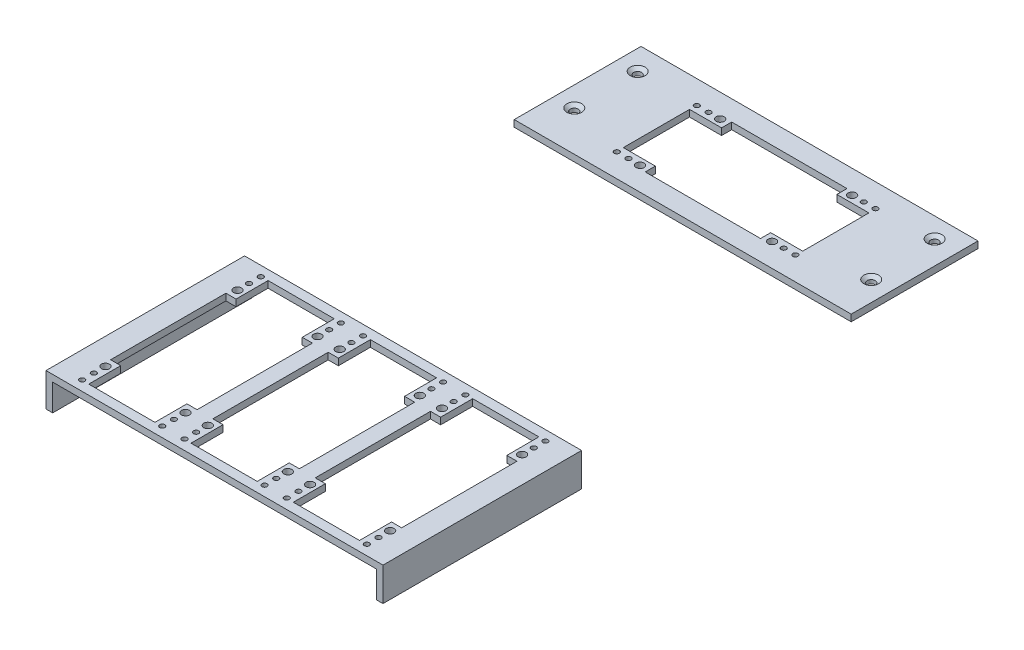
SolidWorks part; units mm, degrees
ref_plane "Front Plane" through (0, 0, 0) normal (0, 0, 1) x (1, 0, 0)
ref_plane "Top Plane" through (0, 0, 0) normal (0, 1, 0) x (1, 0, 0)
ref_plane "Right Plane" through (0, 0, 0) normal (1, 0, 0) x (0, 0, -1)
sketch "Sketch1" plane through (0, 0, 0) normal (0, 1, 0) x (1, 0, 0)
  line L0 (37.4967, 30.1625) -> (0, 30.1625) construction
  line L1 (0, 0) -> (160.3375, 0)
  line L2 (0, 0) -> (0, 60.325)
  line L3 (0, 60.325) -> (160.3375, 60.325)
  line L4 (160.3375, 0) -> (160.3375, 60.325)
  line L5 (122.8408, 30.1625) -> (160.3375, 30.1625) construction
  line L6 (80.1687, 50.7365) -> (80.1687, 60.325) construction
  line L7 (80.1687, 9.5885) -> (80.1687, 0) construction
  line L8 (29.5195, -167.5613) -> (-7.9773, -167.5613) construction
  line L9 (-7.9773, -214.8053) -> (152.3602, -214.8053)
  line L10 (-7.9773, -214.8053) -> (-7.9773, -120.3173)
  line L11 (-7.9773, -120.3173) -> (152.3602, -120.3173)
  line L12 (152.3602, -214.8053) -> (152.3602, -120.3173)
  line L13 (114.8635, -167.5613) -> (152.3602, -167.5613) construction
  line L14 (72.1915, -129.9058) -> (72.1915, -120.3173) construction
  line L15 (72.1915, -205.2168) -> (72.1915, -214.8053) construction
  circle A0 centre (9.525, 49.2125) radius 0.254
  circle A1 centre (9.525, 19.05) radius 0.254
  circle A2 centre (149.225, 50.8) radius 0.254
  circle A3 centre (150.8125, 19.05) radius 0.254
  point P13 (9.525, 49.2125)
  point P14 (9.525, 19.05)
  point P15 (150.8125, 19.05)
  point P16 (149.225, 50.8)
  dimension "D11" = 160.3375
  dimension "D1" = 160.3375
  dimension "D2" = 60.325
  dimension "D3" = 11.1125
  dimension "D4" = 9.525
  dimension "D5" = 9.525
  dimension "D6" = 19.05
  dimension "D7" = 9.525
  dimension "D8" = 11.1125
  dimension "D9" = 9.525
  dimension "D10" = 19.05
  dimension "D12" = 94.488
extrude "Boss-Extrude1" add sketch "Sketch1" along normal blind 3.175
hole_wizard "CSK for #6 Flat Head Machine Screw (100)2" positions "Sketch11" profile "Sketch12" countersink size "#6" standard "ANSI Inch" end condition through all
sketch "Sketch11" plane through (0, 3.175, 0) normal (0, 1, 0) x (1, 0, 0)
  point P0 (9.525, 49.2125)
  point P3 (9.525, 19.05)
  point P6 (149.225, 50.8)
  point P9 (150.8125, 19.05)
sketch "Sketch12" plane through (9.525, 3.175, -49.2125) normal (1, 0, 0) x (0, 0, 1)
  line L0 (0, 0) -> (0, 3.175)
  line L1 (0, 3.175) -> (1.8986, 3.175)
  line L2 (1.8986, 3.175) -> (1.8986, 1.38)
  line L3 (1.8986, 1.38) -> (3.5433, 0)
  line L5 (3.5433, 0) -> (0, 0)
  line L6 (-1.8986, 1.38) -> (-3.5433, 0) construction
  line L11 (0, -6.35) -> (0, 107.95) construction
  dimension "Thru Hole Dia." = 3.7973
  dimension "Thru Hole Depth" = 3.175
  dimension "Near C'Sink Dia." = 7.0866
  dimension "Near C'Sink Angle" = 100
sketch "Sketch14" plane through (0, 3.175, 0) normal (0, 1, 0) x (1, 0, 0)
  line L0 (37.4968, 30.1625) -> (0, 30.1625) construction
  line L1 (152.3602, -120.3173) -> (-7.9773, -120.3173) construction
  line L2 (0, 60.325) -> (0, 0) construction
  line L4 (122.8407, 30.1625) -> (160.3375, 30.1625) construction
  line L6 (160.3375, 0) -> (160.3375, 60.325) construction
  line L8 (80.1688, 50.7365) -> (80.1688, 60.325) construction
  line L9 (160.3375, 60.325) -> (0, 60.325) construction
  line L10 (80.1688, 9.5885) -> (80.1688, 0) construction
  line L11 (0, 0) -> (160.3375, 0) construction
  line L12 (44.0928, -167.5613) -> (51.6175, -167.5613) construction
  line L13 (92.7655, -167.5613) -> (100.2901, -167.5613) construction
  line L14 (2.9448, -167.5613) -> (-7.9773, -167.5613) construction
  line L15 (-7.9773, -120.3173) -> (-7.9773, -214.8053) construction
  line L16 (141.4381, -167.5613) -> (152.3602, -167.5613) construction
  line L17 (152.3602, -214.8053) -> (152.3602, -120.3173) construction
  line L18 (72.1915, -124.8893) -> (72.1915, -120.3173)
  line L20 (72.1915, -210.2333) -> (72.1915, -214.8053)
  line L23 (-7.9773, -214.8053) -> (152.3602, -214.8053) construction
  point P30 (0, 0)
  line B0 (7.7708, -124.8893) -> (39.2668, -124.8893)
  line B1 (7.7708, -124.8893) -> (7.7708, -140.1293)
  line B2 (7.7708, -140.1293) -> (2.9448, -140.1293)
  line B3 (2.9448, -140.1293) -> (2.9448, -194.9933)
  line B4 (2.9448, -194.9933) -> (7.7708, -194.9933)
  line B5 (7.7708, -194.9933) -> (7.7708, -210.2333)
  line B6 (7.7708, -210.2333) -> (39.2668, -210.2333)
  line B7 (39.2668, -210.2333) -> (39.2668, -194.9933)
  line B8 (39.2668, -194.9933) -> (44.0928, -194.9933)
  line B9 (44.0928, -194.9933) -> (44.0928, -140.1293)
  line B10 (44.0928, -140.1293) -> (39.2668, -140.1293)
  line B11 (39.2668, -140.1293) -> (39.2668, -124.8893)
  line B12 (42.5688, -138.0719) -> (42.5688, -140.1293) construction
  line B13 (4.4688, -136.8785) -> (4.4688, -138.9359) construction
  circle B14 centre (4.4688, -198.9557) radius 1.905
  circle B15 centre (42.5688, -136.1669) radius 1.905
  circle B16 centre (4.4688, -136.1669) radius 1.905
  circle B17 centre (4.4688, -204.4929) radius 1.2192
  circle B18 centre (4.4688, -210.0555) radius 1.2192
  circle B19 centre (42.5688, -198.9557) radius 1.905
  circle B20 centre (42.5688, -204.4929) radius 1.2192
  circle B21 centre (42.5688, -210.0555) radius 1.2192
  circle B22 centre (42.5688, -130.6297) radius 1.2192
  circle B23 centre (42.5688, -125.0671) radius 1.2192
  circle B24 centre (4.4688, -130.6297) radius 1.2192
  circle B25 centre (4.4688, -125.0671) radius 1.2192
  line B26 (122.8408, 45.9105) -> (122.8408, 14.4145)
  line B27 (122.8408, 45.9105) -> (107.6007, 45.9105)
  line B28 (107.6007, 45.9105) -> (107.6007, 50.7365)
  line B29 (107.6007, 50.7365) -> (52.7368, 50.7365)
  line B30 (52.7368, 50.7365) -> (52.7368, 45.9105)
  line B31 (52.7368, 45.9105) -> (37.4967, 45.9105)
  line B32 (37.4967, 45.9105) -> (37.4968, 14.4145)
  line B33 (37.4968, 14.4145) -> (52.7368, 14.4145)
  line B34 (52.7368, 14.4145) -> (52.7368, 9.5885)
  line B35 (52.7368, 9.5885) -> (107.6008, 9.5885)
  line B36 (107.6008, 9.5885) -> (107.6008, 14.4145)
  line B37 (107.6008, 14.4145) -> (122.8408, 14.4145)
  line B38 (109.6582, 11.1125) -> (107.6008, 11.1125) construction
  line B39 (110.8515, 49.2125) -> (108.7941, 49.2125) construction
  circle B40 centre (48.7744, 49.2125) radius 1.905
  circle B41 centre (111.5632, 11.1125) radius 1.905
  circle B42 centre (111.5631, 49.2125) radius 1.905
  circle B43 centre (43.2372, 49.2125) radius 1.2192
  circle B44 centre (37.6746, 49.2125) radius 1.2192
  circle B45 centre (48.7744, 11.1125) radius 1.905
  circle B46 centre (43.2372, 11.1125) radius 1.2192
  circle B47 centre (37.6746, 11.1125) radius 1.2192
  circle B48 centre (117.1004, 11.1125) radius 1.2192
  circle B49 centre (122.663, 11.1125) radius 1.2192
  circle B50 centre (117.1003, 49.2125) radius 1.2192
  circle B51 centre (122.6629, 49.2125) radius 1.2192
  line B52 (56.4435, -124.8893) -> (87.9395, -124.8893)
  line B53 (56.4435, -124.8893) -> (56.4435, -140.1293)
  line B54 (56.4435, -140.1293) -> (51.6175, -140.1293)
  line B55 (51.6175, -140.1293) -> (51.6175, -194.9933)
  line B56 (51.6175, -194.9933) -> (56.4435, -194.9933)
  line B57 (56.4435, -194.9933) -> (56.4435, -210.2333)
  line B58 (56.4435, -210.2333) -> (87.9395, -210.2333)
  line B59 (87.9395, -210.2333) -> (87.9395, -194.9933)
  line B60 (87.9395, -194.9933) -> (92.7655, -194.9933)
  line B61 (92.7655, -194.9933) -> (92.7655, -140.1293)
  line B62 (92.7655, -140.1293) -> (87.9395, -140.1293)
  line B63 (87.9395, -140.1293) -> (87.9395, -124.8893)
  line B64 (91.2415, -138.0719) -> (91.2415, -140.1293) construction
  line B65 (53.1415, -136.8785) -> (53.1415, -138.9359) construction
  circle B66 centre (53.1415, -198.9557) radius 1.905
  circle B67 centre (91.2415, -136.1669) radius 1.905
  circle B68 centre (53.1415, -136.1669) radius 1.905
  circle B69 centre (53.1415, -204.4929) radius 1.2192
  circle B70 centre (53.1415, -210.0555) radius 1.2192
  circle B71 centre (91.2415, -198.9557) radius 1.905
  circle B72 centre (91.2415, -204.4929) radius 1.2192
  circle B73 centre (91.2415, -210.0555) radius 1.2192
  circle B74 centre (91.2415, -130.6297) radius 1.2192
  circle B75 centre (91.2415, -125.0671) radius 1.2192
  circle B76 centre (53.1415, -130.6297) radius 1.2192
  circle B77 centre (53.1415, -125.0671) radius 1.2192
  line B78 (105.1161, -124.8893) -> (136.6121, -124.8893)
  line B79 (105.1161, -124.8893) -> (105.1161, -140.1293)
  line B80 (105.1161, -140.1293) -> (100.2901, -140.1293)
  line B81 (100.2901, -140.1293) -> (100.2901, -194.9933)
  line B82 (100.2901, -194.9933) -> (105.1161, -194.9933)
  line B83 (105.1161, -194.9933) -> (105.1161, -210.2333)
  line B84 (105.1161, -210.2333) -> (136.6121, -210.2333)
  line B85 (136.6121, -210.2333) -> (136.6121, -194.9933)
  line B86 (136.6121, -194.9933) -> (141.4381, -194.9933)
  line B87 (141.4381, -194.9933) -> (141.4381, -140.1293)
  line B88 (141.4381, -140.1293) -> (136.6121, -140.1293)
  line B89 (136.6121, -140.1293) -> (136.6121, -124.8893)
  line B90 (139.9141, -138.0719) -> (139.9141, -140.1293) construction
  line B91 (101.8141, -136.8785) -> (101.8141, -138.9359) construction
  circle B92 centre (101.8141, -198.9557) radius 1.905
  circle B93 centre (139.9141, -136.1669) radius 1.905
  circle B94 centre (101.8141, -136.1669) radius 1.905
  circle B95 centre (101.8141, -204.4929) radius 1.2192
  circle B96 centre (101.8141, -210.0555) radius 1.2192
  circle B97 centre (139.9141, -198.9557) radius 1.905
  circle B98 centre (139.9141, -204.4929) radius 1.2192
  circle B99 centre (139.9141, -210.0555) radius 1.2192
  circle B100 centre (139.9141, -130.6297) radius 1.2192
  circle B101 centre (139.9141, -125.0671) radius 1.2192
  circle B102 centre (101.8141, -130.6297) radius 1.2192
  circle B103 centre (101.8141, -125.0671) radius 1.2192
sketch_block_instance "Block3-1"
sketch_block "Block3" parameters "D7"=2.4384, "D14"=3.81, "D1"=85.344, "D2"=31.496, "D3"=38.1, "D4"=62.7888, "D5"=5.5372, "D6"=5.5626, "D8"=5.5372, "D9"=5.5626, "D10"=5.5372, "D11"=5.5372, "D12"=4.826, "D13"=3.302, "D15"=5.5626
sketch_block_instance "Block3-2"
sketch_block_instance "Block3-4"
sketch_block_instance "Block3-5"
sketch "Sketch15" plane through (0, 0, 0) normal (0, -1, 0) x (-1, 0, 0)
  line L0 (7.9773, -214.8053) -> (-152.3602, -214.8053) construction
  line L1 (-152.3602, -120.3173) -> (-149.1852, -120.3173)
  line L2 (-152.3602, -120.3173) -> (-152.3602, -214.8053)
  line L3 (-152.3602, -214.8053) -> (-149.1852, -214.8053)
  line L4 (-149.1852, -120.3173) -> (-149.1852, -214.8053)
  line L6 (7.9773, -120.3173) -> (4.8023, -120.3173)
  line L7 (7.9773, -120.3173) -> (7.9773, -214.8053)
  line L8 (7.9773, -214.8053) -> (4.8023, -214.8053)
  line L9 (4.8023, -120.3173) -> (4.8023, -214.8053)
  dimension "D1" = 3.175
extrude "Boss-Extrude2" add sketch "Sketch15" along normal blind 12.7
sketch "Sketch19" plane through (0, 3.175, 0) normal (0, 1, 0) x (1, 0, 0)
  line L0 (7.7708, -124.8893) -> (39.2668, -124.8893) construction
  line L1 (7.7708, -210.2333) -> (39.2668, -210.2333) construction
  line L2 (7.7708, -194.9933) -> (7.7708, -210.2333) construction
  line L3 (2.9448, -194.9933) -> (7.7708, -194.9933) construction
  line L4 (39.2668, -210.2333) -> (39.2668, -194.9933) construction
  line L5 (39.2668, -194.9933) -> (44.0928, -194.9933) construction
  line L6 (44.0928, -194.9933) -> (44.0928, -140.1293) construction
  line L7 (44.0928, -140.1293) -> (39.2668, -140.1293) construction
  line L8 (39.2668, -140.1293) -> (39.2668, -124.8893) construction
  line L9 (7.7708, -124.8893) -> (7.7708, -140.1293) construction
  line L10 (7.7708, -140.1293) -> (2.9448, -140.1293) construction
  line L11 (2.9448, -140.1293) -> (2.9448, -194.9933) construction
  line L12 (7.7708, -124.8893) -> (39.2668, -124.8893)
  line L13 (7.7708, -210.2333) -> (39.2668, -210.2333)
  line L14 (7.7708, -194.9933) -> (7.7708, -210.2333)
  line L15 (2.9448, -194.9933) -> (7.7708, -194.9933)
  line L16 (39.2668, -210.2333) -> (39.2668, -194.9933)
  line L17 (39.2668, -194.9933) -> (44.0928, -194.9933)
  line L18 (44.0928, -194.9933) -> (44.0928, -140.1293)
  line L19 (44.0928, -140.1293) -> (39.2668, -140.1293)
  line L20 (39.2668, -140.1293) -> (39.2668, -124.8893)
  line L21 (7.7708, -124.8893) -> (7.7708, -140.1293)
  line L22 (7.7708, -140.1293) -> (2.9448, -140.1293)
  line L23 (2.9448, -140.1293) -> (2.9448, -194.9933)
  line L24 (141.4381, -140.1293) -> (136.6121, -140.1293) construction
  line L25 (136.6121, -140.1293) -> (136.6121, -124.8893) construction
  line L26 (105.1161, -124.8893) -> (136.6121, -124.8893) construction
  line L27 (105.1161, -124.8893) -> (105.1161, -140.1293) construction
  line L28 (105.1161, -140.1293) -> (100.2901, -140.1293) construction
  line L29 (136.6121, -194.9933) -> (141.4381, -194.9933) construction
  line L30 (141.4381, -194.9933) -> (141.4381, -140.1293) construction
  line L31 (136.6121, -210.2333) -> (136.6121, -194.9933) construction
  line L32 (100.2901, -140.1293) -> (100.2901, -194.9933) construction
  line L33 (100.2901, -194.9933) -> (105.1161, -194.9933) construction
  line L34 (105.1161, -194.9933) -> (105.1161, -210.2333) construction
  line L35 (105.1161, -210.2333) -> (136.6121, -210.2333) construction
  line L36 (56.4435, -210.2333) -> (87.9395, -210.2333) construction
  line L37 (87.9395, -210.2333) -> (87.9395, -194.9933) construction
  line L38 (56.4435, -194.9933) -> (56.4435, -210.2333) construction
  line L39 (51.6175, -194.9933) -> (56.4435, -194.9933) construction
  line L40 (87.9395, -194.9933) -> (92.7655, -194.9933) construction
  line L41 (51.6175, -140.1293) -> (51.6175, -194.9933) construction
  line L42 (92.7655, -194.9933) -> (92.7655, -140.1293) construction
  line L43 (92.7655, -140.1293) -> (87.9395, -140.1293) construction
  line L44 (87.9395, -140.1293) -> (87.9395, -124.8893) construction
  line L45 (56.4435, -124.8893) -> (56.4435, -140.1293) construction
  line L46 (56.4435, -140.1293) -> (51.6175, -140.1293) construction
  line L47 (56.4435, -124.8893) -> (87.9395, -124.8893) construction
  line L48 (141.4381, -140.1293) -> (136.6121, -140.1293)
  line L49 (136.6121, -140.1293) -> (136.6121, -124.8893)
  line L50 (105.1161, -124.8893) -> (136.6121, -124.8893)
  line L51 (105.1161, -124.8893) -> (105.1161, -140.1293)
  line L52 (105.1161, -140.1293) -> (100.2901, -140.1293)
  line L53 (136.6121, -194.9933) -> (141.4381, -194.9933)
  line L54 (141.4381, -194.9933) -> (141.4381, -140.1293)
  line L55 (136.6121, -210.2333) -> (136.6121, -194.9933)
  line L56 (100.2901, -140.1293) -> (100.2901, -194.9933)
  line L57 (100.2901, -194.9933) -> (105.1161, -194.9933)
  line L58 (105.1161, -194.9933) -> (105.1161, -210.2333)
  line L59 (105.1161, -210.2333) -> (136.6121, -210.2333)
  line L60 (56.4435, -210.2333) -> (87.9395, -210.2333)
  line L61 (87.9395, -210.2333) -> (87.9395, -194.9933)
  line L62 (56.4435, -194.9933) -> (56.4435, -210.2333)
  line L63 (51.6175, -194.9933) -> (56.4435, -194.9933)
  line L64 (87.9395, -194.9933) -> (92.7655, -194.9933)
  line L65 (51.6175, -140.1293) -> (51.6175, -194.9933)
  line L66 (92.7655, -194.9933) -> (92.7655, -140.1293)
  line L67 (92.7655, -140.1293) -> (87.9395, -140.1293)
  line L68 (87.9395, -140.1293) -> (87.9395, -124.8893)
  line L69 (56.4435, -124.8893) -> (56.4435, -140.1293)
  line L70 (56.4435, -140.1293) -> (51.6175, -140.1293)
  line L71 (56.4435, -124.8893) -> (87.9395, -124.8893)
  line L72 (122.8408, 45.9105) -> (107.6007, 45.9105) construction
  line L73 (122.8408, 45.9105) -> (122.8408, 14.4145) construction
  line L74 (107.6008, 14.4145) -> (122.8408, 14.4145) construction
  line L75 (107.6008, 9.5885) -> (107.6008, 14.4145) construction
  line L76 (52.7368, 9.5885) -> (107.6008, 9.5885) construction
  line L77 (52.7368, 14.4145) -> (52.7368, 9.5885) construction
  line L78 (37.4968, 14.4145) -> (52.7368, 14.4145) construction
  line L79 (37.4967, 45.9105) -> (37.4968, 14.4145) construction
  line L80 (52.7368, 45.9105) -> (37.4967, 45.9105) construction
  line L81 (52.7368, 50.7365) -> (52.7368, 45.9105) construction
  line L82 (107.6007, 50.7365) -> (52.7368, 50.7365) construction
  line L83 (122.8408, 45.9105) -> (107.6007, 45.9105)
  line L84 (122.8408, 45.9105) -> (122.8408, 14.4145)
  line L85 (107.6008, 14.4145) -> (122.8408, 14.4145)
  line L86 (107.6008, 9.5885) -> (107.6008, 14.4145)
  line L87 (52.7368, 9.5885) -> (107.6008, 9.5885)
  line L88 (52.7368, 14.4145) -> (52.7368, 9.5885)
  line L89 (37.4968, 14.4145) -> (52.7368, 14.4145)
  line L90 (37.4967, 45.9105) -> (37.4968, 14.4145)
  line L91 (52.7368, 45.9105) -> (37.4967, 45.9105)
  line L92 (52.7368, 50.7365) -> (52.7368, 45.9105)
  line L93 (107.6007, 50.7365) -> (52.7368, 50.7365)
  line L94 (107.6007, 45.9105) -> (107.6007, 50.7365) construction
  line L95 (107.6007, 45.9105) -> (107.6007, 50.7365)
  circle A0 centre (42.5688, -136.1669) radius 1.905 construction
  circle A1 centre (42.5688, -130.6297) radius 1.2192 construction
  circle A2 centre (42.5688, -125.0671) radius 1.2192 construction
  circle A3 centre (4.4688, -136.1669) radius 1.905 construction
  circle A4 centre (4.4688, -130.6297) radius 1.2192 construction
  circle A5 centre (4.4688, -125.0671) radius 1.2192 construction
  circle A6 centre (42.5688, -210.0555) radius 1.2192 construction
  circle A7 centre (42.5688, -204.4929) radius 1.2192 construction
  circle A8 centre (42.5688, -198.9557) radius 1.905 construction
  circle A9 centre (4.4688, -210.0555) radius 1.2192 construction
  circle A10 centre (4.4688, -204.4929) radius 1.2192 construction
  circle A11 centre (4.4688, -198.9557) radius 1.905 construction
  circle A12 centre (42.5688, -136.1669) radius 1.905
  circle A13 centre (42.5688, -130.6297) radius 1.2192
  circle A14 centre (42.5688, -125.0671) radius 1.2192
  circle A15 centre (4.4688, -136.1669) radius 1.905
  circle A16 centre (4.4688, -130.6297) radius 1.2192
  circle A17 centre (4.4688, -125.0671) radius 1.2192
  circle A18 centre (42.5688, -210.0555) radius 1.2192
  circle A19 centre (42.5688, -204.4929) radius 1.2192
  circle A20 centre (42.5688, -198.9557) radius 1.905
  circle A21 centre (4.4688, -210.0555) radius 1.2192
  circle A22 centre (4.4688, -204.4929) radius 1.2192
  circle A23 centre (4.4688, -198.9557) radius 1.905
  circle A24 centre (139.9141, -125.0671) radius 1.2192 construction
  circle A25 centre (139.9141, -130.6297) radius 1.2192 construction
  circle A26 centre (139.9141, -136.1669) radius 1.905 construction
  circle A27 centre (101.8141, -136.1669) radius 1.905 construction
  circle A28 centre (101.8141, -130.6297) radius 1.2192 construction
  circle A29 centre (101.8141, -125.0671) radius 1.2192 construction
  circle A30 centre (91.2415, -136.1669) radius 1.905 construction
  circle A31 centre (91.2415, -130.6297) radius 1.2192 construction
  circle A32 centre (91.2415, -125.0671) radius 1.2192 construction
  circle A33 centre (139.9141, -210.0555) radius 1.2192 construction
  circle A34 centre (139.9141, -204.4929) radius 1.2192 construction
  circle A35 centre (139.9141, -198.9557) radius 1.905 construction
  circle A36 centre (101.8141, -210.0555) radius 1.2192 construction
  circle A37 centre (101.8141, -204.4929) radius 1.2192 construction
  circle A38 centre (101.8141, -198.9557) radius 1.905 construction
  circle A39 centre (91.2415, -210.0555) radius 1.2192 construction
  circle A40 centre (91.2415, -204.4929) radius 1.2192 construction
  circle A41 centre (91.2415, -198.9557) radius 1.905 construction
  circle A42 centre (53.1415, -198.9557) radius 1.905 construction
  circle A43 centre (53.1415, -204.4929) radius 1.2192 construction
  circle A44 centre (53.1415, -210.0555) radius 1.2192 construction
  circle A45 centre (53.1415, -136.1669) radius 1.905 construction
  circle A46 centre (53.1415, -130.6297) radius 1.2192 construction
  circle A47 centre (53.1415, -125.0671) radius 1.2192 construction
  circle A48 centre (139.9141, -125.0671) radius 1.2192
  circle A49 centre (139.9141, -130.6297) radius 1.2192
  circle A50 centre (139.9141, -136.1669) radius 1.905
  circle A51 centre (101.8141, -136.1669) radius 1.905
  circle A52 centre (101.8141, -130.6297) radius 1.2192
  circle A53 centre (101.8141, -125.0671) radius 1.2192
  circle A54 centre (91.2415, -136.1669) radius 1.905
  circle A55 centre (91.2415, -130.6297) radius 1.2192
  circle A56 centre (91.2415, -125.0671) radius 1.2192
  circle A57 centre (139.9141, -210.0555) radius 1.2192
  circle A58 centre (139.9141, -204.4929) radius 1.2192
  circle A59 centre (139.9141, -198.9557) radius 1.905
  circle A60 centre (101.8141, -210.0555) radius 1.2192
  circle A61 centre (101.8141, -204.4929) radius 1.2192
  circle A62 centre (101.8141, -198.9557) radius 1.905
  circle A63 centre (91.2415, -210.0555) radius 1.2192
  circle A64 centre (91.2415, -204.4929) radius 1.2192
  circle A65 centre (91.2415, -198.9557) radius 1.905
  circle A66 centre (53.1415, -198.9557) radius 1.905
  circle A67 centre (53.1415, -204.4929) radius 1.2192
  circle A68 centre (53.1415, -210.0555) radius 1.2192
  circle A69 centre (53.1415, -136.1669) radius 1.905
  circle A70 centre (53.1415, -130.6297) radius 1.2192
  circle A71 centre (53.1415, -125.0671) radius 1.2192
  circle A72 centre (37.6746, 49.2125) radius 1.2192 construction
  circle A73 centre (43.2372, 49.2125) radius 1.2192 construction
  circle A74 centre (48.7744, 49.2125) radius 1.905 construction
  circle A75 centre (37.6746, 11.1125) radius 1.2192 construction
  circle A76 centre (43.2372, 11.1125) radius 1.2192 construction
  circle A77 centre (48.7744, 11.1125) radius 1.905 construction
  circle A78 centre (111.5632, 11.1125) radius 1.905 construction
  circle A79 centre (117.1004, 11.1125) radius 1.2192 construction
  circle A80 centre (122.663, 11.1125) radius 1.2192 construction
  circle A81 centre (122.6629, 49.2125) radius 1.2192 construction
  circle A82 centre (117.1003, 49.2125) radius 1.2192 construction
  circle A83 centre (111.5631, 49.2125) radius 1.905 construction
  circle A84 centre (37.6746, 49.2125) radius 1.2192
  circle A85 centre (43.2372, 49.2125) radius 1.2192
  circle A86 centre (48.7744, 49.2125) radius 1.905
  circle A87 centre (37.6746, 11.1125) radius 1.2192
  circle A88 centre (43.2372, 11.1125) radius 1.2192
  circle A89 centre (48.7744, 11.1125) radius 1.905
  circle A90 centre (111.5632, 11.1125) radius 1.905
  circle A91 centre (117.1004, 11.1125) radius 1.2192
  circle A92 centre (122.663, 11.1125) radius 1.2192
  circle A93 centre (122.6629, 49.2125) radius 1.2192
  circle A94 centre (117.1003, 49.2125) radius 1.2192
  circle A95 centre (111.5631, 49.2125) radius 1.905
extrude "Cut-Extrude1" cut sketch "Sketch19" against normal blind 12.7
